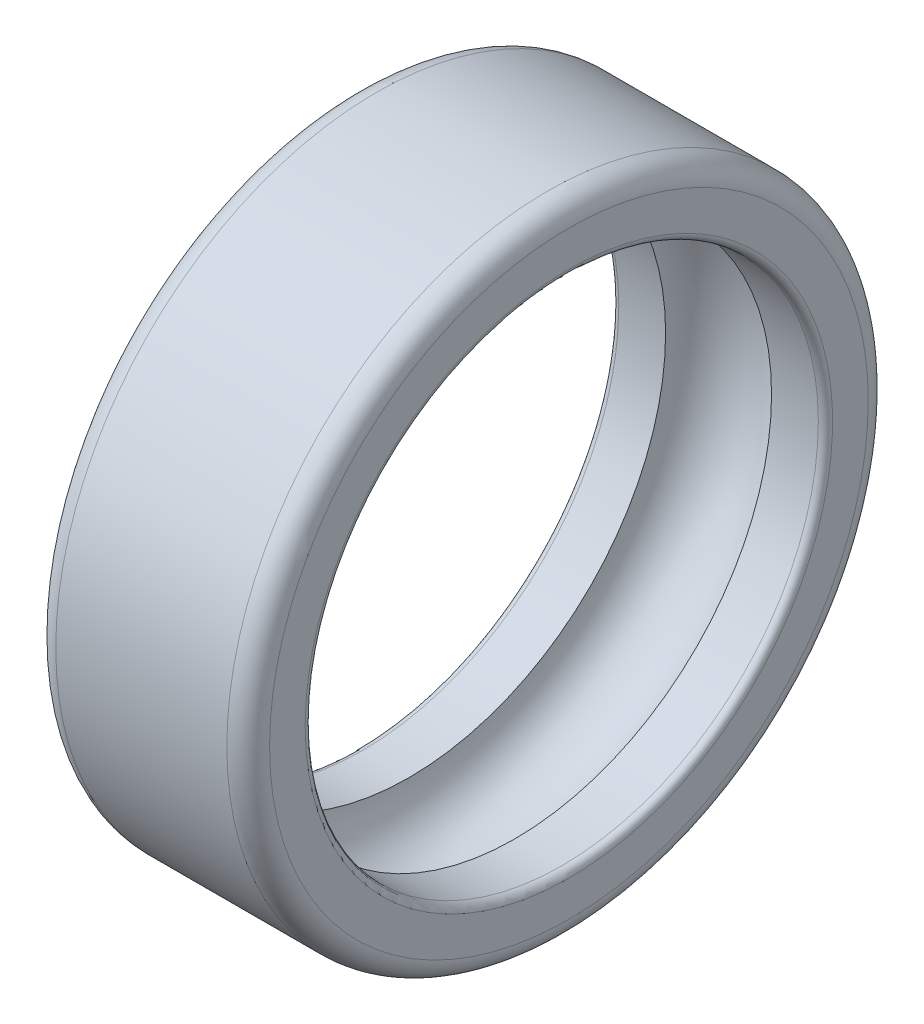
SolidWorks part; units mm, degrees
material "Plain Carbon Steel"
ref_plane "Front Plane" through (0, 0, 0) normal (0, 0, 1) x (1, 0, 0)
ref_plane "Top Plane" through (0, 0, 0) normal (0, 1, 0) x (1, 0, 0)
ref_plane "Right Plane" through (0, 0, 0) normal (1, 0, 0) x (0, 0, -1)
ref_plane "Plane1" through (0, 0, 0) normal (0, 0, -1) x (-1, 0, 0)
sketch "Sketch1" plane through (0, 0, 0) normal (0, 0, -1) x (-1, 0, 0)
  line L0 (-6.9, 16.65) -> (-6.2433, 16.65)
  line L1 (-4.7567, 16.65) -> (-4.1, 16.65)
  line L2 (-4, 16.75) -> (-4, 17.25)
  line L3 (-4.3, 17.55) -> (-6.7, 17.55)
  line L4 (-7, 17.25) -> (-7, 16.75)
  line L5 (-8.0514, 13.05) -> (-2.9486, 13.05) construction
  line L6 (-5.5, 16.55) -> (-5.5, 13.05) construction
  arc A0 (-6.2433, 16.65) -> (-4.7567, 16.65) centre (-5.5, 16.55) cw
  arc A1 (-4.1, 16.65) -> (-4, 16.75) centre (-4.1, 16.75) ccw
  arc A2 (-4, 17.25) -> (-4.3, 17.55) centre (-4.3, 17.25) ccw
  arc A3 (-6.7, 17.55) -> (-7, 17.25) centre (-6.7, 17.25) ccw
  arc A4 (-7, 16.75) -> (-6.9, 16.65) centre (-6.9, 16.75) ccw
  dimension "D3" = 0.75
  dimension "D1" = 9
  dimension "D2" = 7.2
  dimension "D4" = 3
  dimension "D5" = 7
revolve "Revolve1" add sketch "Sketch1" angle 360 about L5
